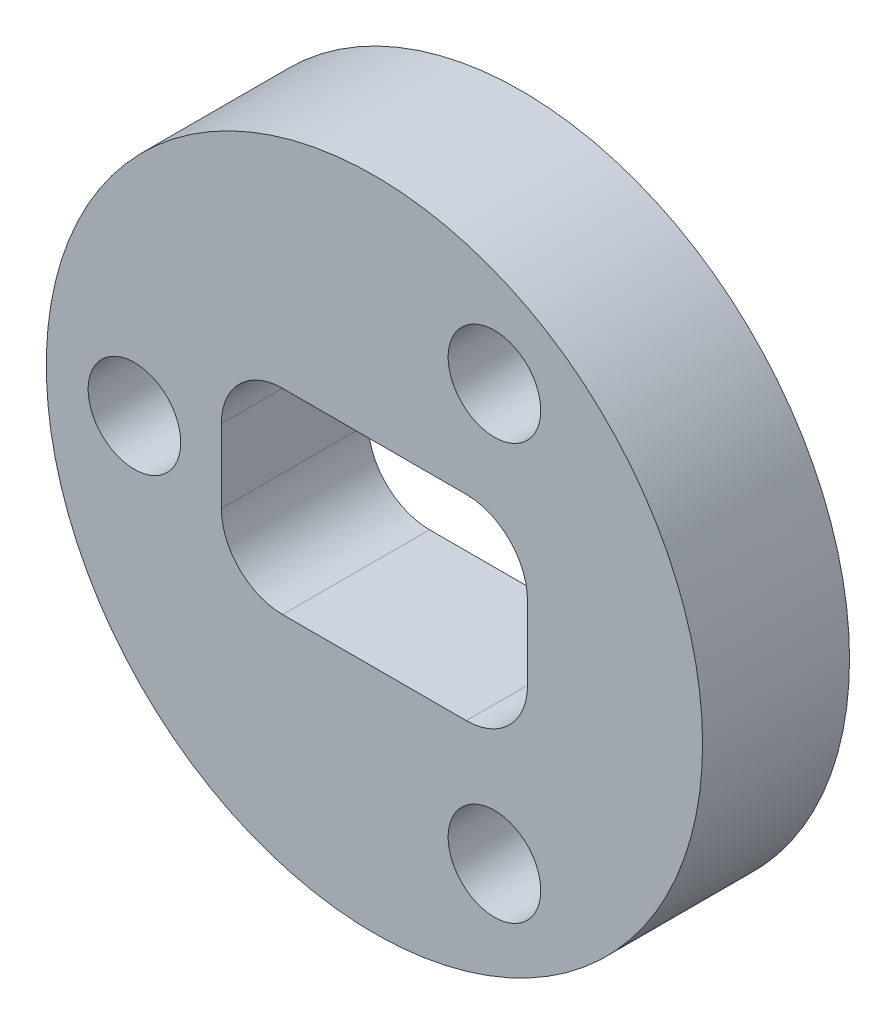
SolidWorks part; units mm, degrees
ref_plane "Front Plane" through (0, 0, 0) normal (0, 0, 1) x (1, 0, 0)
ref_plane "Top Plane" through (0, 0, 0) normal (0, 1, 0) x (1, 0, 0)
ref_plane "Right Plane" through (0, 0, 0) normal (1, 0, 0) x (0, 0, -1)
sketch "Sketch1" plane through (0, 0, 0) normal (0, 0, 1) x (1, 0, 0)
  circle A0 centre (0, 0) radius 8.509
  dimension "D1" = 17.018
extrude "Boss-Extrude1" add sketch "Sketch1" along normal blind 3.81
ref_plane "Plane1" through (0, 0, 3.81) normal (0, 0, 1) x (1, 0, 0)
sketch "Sketch2" plane through (0, 0, 3.81) normal (0, 0, 1) x (1, 0, 0)
  line L0 (-8.509, 0) -> (8.509, 0) construction
  circle A0 centre (0, 0) radius 6.223 construction
  circle A1 centre (0, 0) radius 8.509 construction
  circle A2 centre (-6.223, 0) radius 1.143
  circle A3 centre (3.1115, 5.3893) radius 1.143
  circle A4 centre (3.1115, -5.3893) radius 1.143
  point P16 (0, 0)
  dimension "D1" = 12.446
  dimension "D2" = 2.286
  dimension "D4" = 3.1115
  dimension "D5" = 5.3893
  dimension "D3" = 3
sketch "Sketch3" plane through (0, 0, 3.81) normal (0, 0, 1) x (1, 0, 0)
  line L0 (-8.509, 0) -> (8.509, 0) construction
  line L1 (-3.9688, 2.54) -> (3.9688, 2.54)
  line L2 (-3.9688, 2.54) -> (-3.9688, -2.54)
  line L3 (-3.9688, -2.54) -> (3.9687, -2.54)
  line L4 (3.9688, 2.54) -> (3.9687, -2.54)
  circle A0 centre (0, 0) radius 8.509 construction
  dimension "D1" = 5.08
  dimension "D2" = 3.9688
  dimension "D3" = 7.9375
  dimension "D4" = 2.54
extrude "Cut-Extrude2" cut sketch "Sketch3" against normal blind 3.81
hole_wizard "M2 Clearance Hole1" positions "Sketch4" profile "Sketch5" hole size "M2" standard "ANSI Metric" end condition through all
sketch "Sketch4" plane through (0, 0, 3.81) normal (0, 0, 1) x (1, 0, 0)
  point P0 (-6.223, 0)
  point P3 (3.1115, 5.3893)
  point P6 (3.1115, -5.3893)
sketch "Sketch5" plane through (-6.223, 0, 3.81) normal (1, 0, 0) x (0, -1, 0)
  line L0 (0, 0) -> (0, 3.81)
  line L1 (0, 3.81) -> (1.2, 3.81)
  line L2 (1.2, 3.81) -> (1.2, 0)
  line L5 (1.2, 0) -> (0, 0)
  line L11 (0, -6.35) -> (0, 107.95) construction
  dimension "Thru Hole Dia." = 2.4
  dimension "Thru Hole Depth" = 3.81
fillet "Fillet1" radius 1.5875 4 edges at (3.9687, -2.54, 1.905) (-3.9688, -2.54, 1.905) (3.9688, 2.54, 1.905) (-3.9688, 2.54, 1.905)
